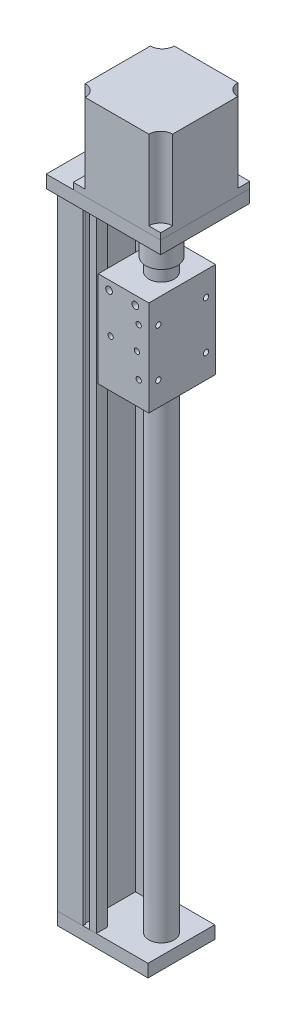
SolidWorks part; units mm, degrees
ref_plane "Front Plane" through (0, 0, 0) normal (0, 0, 1) x (1, 0, 0)
ref_plane "Top Plane" through (0, 0, 0) normal (0, 1, 0) x (1, 0, 0)
ref_plane "Right Plane" through (0, 0, 0) normal (1, 0, 0) x (0, 0, -1)
sketch "Sketch1" plane through (0, 0, 0) normal (0, 1, 0) x (1, 0, 0)
  line L1 (0, 21) -> (57, 21)
  line L2 (0, 21) -> (0, -21)
  line L3 (0, -21) -> (57, -21)
  line L4 (57, 21) -> (57, -21)
  point P4 (0, 0)
  dimension "D1" = 57
  dimension "D2" = 42
extrude "Boss-Extrude1" add sketch "Sketch1" along normal blind 8
sketch "Sketch2" plane through (0, 8, 0) normal (0, 1, 0) x (1, 0, 0)
  line L0 (0, 21) -> (0, -21)
  line L1 (0, -21) -> (24.5, -21)
  line L2 (0, -21) -> (57, -21) construction
  line L3 (24.5, -21) -> (24.5, -14)
  line L4 (24.5, -14) -> (14.1, -14)
  line L5 (14.1, -14) -> (14.1, 14)
  line L6 (14.1, 14) -> (24.5, 14)
  line L7 (24.5, 14) -> (24.5, 21)
  line L8 (57, 21) -> (0, 21) construction
  line L9 (24.5, 21) -> (0, 21)
  dimension "D1" = 24.5
  dimension "D2" = 7
  dimension "D3" = 10.4
extrude "Boss-Extrude2" add sketch "Sketch2" along normal blind 397
sketch "Sketch3" plane through (0, 405, 0) normal (0, 1, 0) x (1, 0, 0)
  line L1 (0, 28) -> (72, 28)
  line L2 (0, 28) -> (0, -28)
  line L3 (0, -28) -> (72, -28)
  line L4 (72, 28) -> (72, -28)
  point P4 (0, 0)
  dimension "D1" = 56
  dimension "D2" = 72
extrude "Boss-Extrude3" add sketch "Sketch3" along normal blind 8
sketch "Sketch4" plane through (0, 413, 0) normal (0, 1, 0) x (1, 0, 0)
  line L0 (0, -28) -> (72, -28) construction
  line L1 (72, 28) -> (17, 28)
  line L2 (72, 28) -> (72, -28)
  line L3 (72, -28) -> (17, -28)
  line L4 (17, 28) -> (17, -28)
  line L5 (57, -21) -> (57, 21) construction
  line L6 (57, -21) -> (57, 21) construction
  point P7 (44.5, 28)
  dimension "D1" = 55
extrude "Boss-Extrude4" add sketch "Sketch4" along normal blind 54
sketch "Sketch5" plane through (0, 467, 0) normal (0, 1, 0) x (1, 0, 0)
  line L0 (17, 28) -> (17, 20.5)
  line L1 (17, 28) -> (17, -28) construction
  line L2 (17, 28) -> (24.5, 28)
  line L3 (44.5, 28) -> (44.5, 12.3616) construction
  line L4 (72, 28) -> (17, 28) construction
  line L5 (72, 28) -> (64.5, 28)
  line L6 (72, 28) -> (72, 20.5)
  line L7 (17, 0) -> (32.1173, 0) construction
  line L8 (72, -28) -> (72, -20.5)
  line L9 (72, -28) -> (64.5, -28)
  line L10 (17, -28) -> (24.5, -28)
  line L11 (17, -28) -> (17, -20.5)
  arc A0 (24.5, 28) -> (17, 20.5) centre (17, 28) cw
  arc A1 (64.5, 28) -> (72, 20.5) centre (72, 28) ccw
  arc A2 (64.5, -28) -> (72, -20.5) centre (72, -28) cw
  arc A3 (24.5, -28) -> (17, -20.5) centre (17, -28) ccw
  dimension "D1" = 7.5
extrude "Cut-Extrude1" cut sketch "Sketch5" against normal blind 50
sketch "Sketch6" plane through (0, 8, 0) normal (0, 1, 0) x (1, 0, 0)
  line L0 (57, -21) -> (57, 21) construction
  circle A0 centre (44.5, 0) radius 8
  point P5 (0, 0)
  dimension "D1" = 16
  dimension "D2" = 12.5
extrude "Boss-Extrude5" add sketch "Sketch6" along normal blind 368.3
ref_plane "Plane1" through (0, 338, 0) normal (0, 1, 0) x (1, 0, 0)
sketch "Sketch7" plane through (0, 338, 0) normal (0, 1, 0) x (1, 0, 0)
  line L0 (24.5, -21) -> (24.5, -14) construction
  line L1 (25.7, -21) -> (57.5, -21)
  line L2 (25.7, -21) -> (25.7, 21)
  line L3 (25.7, 21) -> (57.5, 21)
  line L4 (57.5, -21) -> (57.5, 21)
  line L5 (24.5, -21) -> (57, -21) construction
  line L6 (57, 21) -> (24.5, 21) construction
  line L7 (0, 21) -> (0, -21) construction
  dimension "D1" = 1.2
  dimension "D2" = 57.5
extrude "Boss-Extrude6" add sketch "Sketch7" along normal mid plane 60
sketch "Sketch8" plane through (0, 376.3, 0) normal (0, 1, 0) x (1, 0, 0)
  circle A0 centre (44.5, 0) radius 10
  dimension "D1" = 20
extrude "Boss-Extrude7" add sketch "Sketch8" along normal blind 25
sketch "Sketch9" plane through (0, 405, 0) normal (0, -1, 0) x (1, 0, 0)
  circle A0 centre (44.5, 0) radius 15
  circle A1 centre (44.5, 0) radius 10
  circle A2 centre (44.5, 0) radius 10 construction
  dimension "D2" = 30
  dimension "D1" = 0
extrude "Cut-Extrude2" cut sketch "Sketch9" against normal blind 5
sketch "Sketch10" plane through (0, 401.3, 0) normal (0, 1, 0) x (1, 0, 0)
  circle A0 centre (44.5, 0) radius 3.175
  dimension "D1" = 6.35
extrude "Boss-Extrude8" add sketch "Sketch10" along normal up to next
sketch "Sketch11" plane through (0, 0, -21) normal (0, 0, -1) x (-1, 0, 0)
  line L0 (-24.5, 405) -> (0, 405) construction
  line L1 (-20.3, 405) -> (-16, 405)
  line L2 (-20.3, 405) -> (-20.3, 8)
  line L3 (-20.3, 8) -> (-16, 8)
  line L4 (-16, 405) -> (-16, 8)
  line L5 (-57, 8) -> (-24.5, 8) construction
  line L6 (0, 405) -> (0, 0) construction
  dimension "D1" = 16
  dimension "D2" = 4.3
extrude "Cut-Extrude3" cut sketch "Sketch11" against normal blind 5.4
ref_plane "Plane2" through (18.15, 0, 0) normal (1, 0, 0) x (0, 0, -1)
sketch "Sketch12" plane through (18.15, 0, 0) normal (1, 0, 0) x (0, 0, -1)
  line L0 (15.6, 405) -> (15.6, 8) construction
  line L1 (19.2, 8) -> (15.6, 8)
  line L2 (19.2, 8) -> (19.2, 405)
  line L3 (19.2, 405) -> (15.6, 405)
  line L4 (15.6, 8) -> (15.6, 405)
  line L5 (28, 405) -> (21, 405) construction
  line L6 (15.6, 8) -> (21, 8) construction
  line L7 (21, 405) -> (21, 8) construction
  dimension "D1" = 1.8
extrude "Cut-Extrude4" cut sketch "Sketch12" against normal mid plane 5.4
mirror "Mirror1" about plane through (0, 0, 0) normal (0, 0, 1) of "Cut-Extrude3", "Cut-Extrude4"
sketch "Sketch13" plane through (0, 0, 0) normal (-1, 0, 0) x (0, 0, 1)
  line L0 (21, 8) -> (-21, 8) construction
  line L1 (21, 8) -> (-21, 8) construction
  line L3 (17.15, 405) -> (12.85, 405)
  line L4 (17.15, 405) -> (17.15, 8)
  line L5 (17.15, 8) -> (12.85, 8)
  line L6 (12.85, 405) -> (12.85, 8)
  line L7 (21, 405) -> (28, 405) construction
  line L8 (0, 413) -> (0, 348.5706) construction
  line L9 (-28, 413) -> (28, 413) construction
  point P17 (15, 405)
  dimension "D1" = 15
  dimension "D2" = 4.3
extrude "Cut-Extrude5" cut sketch "Sketch13" against normal blind 6.8
ref_plane "Plane3" through (0, 0, 15) normal (0, 0, 1) x (1, 0, 0)
sketch "Sketch14" plane through (0, 0, 15) normal (0, 0, 1) x (1, 0, 0)
  line L0 (6.8, 405) -> (0, 405) construction
  line L1 (2, 8) -> (5.3, 8)
  line L2 (2, 8) -> (2, 405)
  line L3 (2, 405) -> (5.3, 405)
  line L4 (5.3, 8) -> (5.3, 405)
  line L5 (6.8, 8) -> (0, 8) construction
  line L6 (6.8, 405) -> (6.8, 8) construction
  line L7 (0, 405) -> (0, 8) construction
  dimension "D1" = 1.5
  dimension "D2" = 2
extrude "Cut-Extrude6" cut sketch "Sketch14" against normal mid plane 6.8
mirror "Mirror2" about plane through (0, 0, 0) normal (0, 0, 1) of "Cut-Extrude6", "Cut-Extrude5"
sketch "Sketch15" plane through (57.5, 0, 0) normal (1, 0, 0) x (0, 0, -1)
  line L0 (-21, 368) -> (21, 368) construction
  line L1 (-15, 323) -> (15, 323)
  line L2 (-15, 323) -> (-15, 353)
  line L3 (-15, 353) -> (15, 353)
  line L4 (15, 323) -> (15, 353)
  line L5 (-15, 323) -> (15, 353) construction
  line L6 (-15, 353) -> (15, 323) construction
  line L7 (-21, 368) -> (-21, 308) construction
  point P0 (0, 338)
  point P5 (0, 368)
  point P6 (-21, 338)
  dimension "D1" = 30
  dimension "D2" = 30
hole_wizard "M4x0.7 Tapped Hole1" positions "Sketch19" profile "Sketch18" tap size "M4x0.7" standard "ANSI Metric"
sketch "Sketch19" plane through (57.5, 0, 0) normal (1, 0, 0) x (0, 0, -1)
  point P0 (-15, 353)
  point P3 (15, 353)
  point P6 (15, 323)
  point P9 (-15, 323)
sketch "Sketch18" plane through (57.5, 353, 15) normal (0, 1, 0) x (0, 0, -1)
  line L0 (0, 0) -> (0, 11.0914)
  line L1 (0, 11.0914) -> (1.65, 10.1)
  line L2 (1.65, 10.1) -> (1.65, 0)
  line L5 (1.65, 0) -> (0, 0)
  line L10 (0, 11.0914) -> (-1.65, 10.1) construction
  line L11 (0, -6.35) -> (0, 107.95) construction
  dimension "Tap Drill Dia." = 3.3
  dimension "Tap Drill Depth" = 10.1
  dimension "Drill Angle" = 118
cosmetic thread "Hole Thread1" parameters "D1"=8, "D2"=4
cosmetic thread "Hole Thread2" parameters "D1"=8, "D2"=4
cosmetic thread "Hole Thread3" parameters "D1"=8, "D2"=4
cosmetic thread "Hole Thread4" parameters "D1"=8, "D2"=4
ref_plane "Plane5" through (0, 8, 0) normal (0, 1, 0) x (1, 0, 0)
ref_plane "Plane6" through (0, 413, 0) normal (0, 1, 0) x (1, 0, 0)
ref_plane "Plane7" through (0, 405, 0) normal (0, -1, 0) x (-1, 0, 0)
split line "Split Line4"
split line "Split Line5"
split line "Split Line6"
sketch "Sketch20" plane through (0, 0, 0) normal (0, 0, 1) x (1, 0, 0)
  line L0 (36.5, 376.3) -> (52.5, 376.3) construction
  line L1 (27, 368) -> (62, 368) construction
  line L2 (27, 368) -> (27, 308) construction
  line L3 (27, 308) -> (62, 308) construction
  line L4 (62, 368) -> (62, 308) construction
  line L5 (24.5, 8) -> (57, 8) construction
  line L6 (27, 68) -> (62, 68) construction
  line L7 (27, 68) -> (27, 8) construction
  line L8 (27, 8) -> (62, 8) construction
  line L9 (62, 68) -> (62, 8) construction
  line L10 (44.5, 368) -> (44.5, 68) construction
  line L11 (44.5, 218) -> (94.5, 218)
  line L12 (44.5, 228) -> (94.5, 228) construction
  line L13 (44.5, 208) -> (94.5, 208) construction
  point P4 (44.5, 376.3)
  point P5 (62, 338)
  point P12 (44.5, 68)
  point P19 (62, 38)
  dimension "D1" = 60
  dimension "D2" = 60
  dimension "D3" = 300
  dimension "D4" = 35
  dimension "D5" = 10
  dimension "D6" = 50
  dimension "D7" = 10
sketch "Sketch21" plane through (0, 0, 0) normal (0, 0, 1) x (1, 0, 0)
  line L0 (44.5, 308) -> (44.5, 13.0745) construction
  line L1 (59.5, 89.55) -> (29.5, 89.55)
  line L2 (59.5, 89.55) -> (59.5, 29.55)
  line L3 (59.5, 29.55) -> (29.5, 29.55)
  line L4 (29.5, 89.55) -> (29.5, 29.55)
  line L5 (36.5, 308) -> (52.5, 308) construction
  line L6 (24.5, 8) -> (57, 8) construction
  line L7 (59.5, 329.55) -> (59.5, 59.55) construction
  line L8 (29.5, 359.55) -> (59.5, 359.55)
  line L9 (29.5, 359.55) -> (29.5, 299.55)
  line L10 (29.5, 299.55) -> (59.5, 299.55)
  line L11 (59.5, 359.55) -> (59.5, 299.55)
  line L12 (59.5, 194.55) -> (259.5525, 194.55) construction
  point P8 (44.5, 89.55)
  point P11 (59.5, 59.55)
  point P16 (44.5, 359.55)
  point P17 (59.5, 329.55)
  dimension "D1" = 60
  dimension "D2" = 30
  dimension "D3" = 51.55
  dimension "D4" = 270
sketch "Sketch22" plane through (0, 0, 21) normal (0, 0, 1) x (1, 0, 0)
  line L0 (57.5, 338) -> (25.7, 338) construction
  line L1 (57.5, 368) -> (57.5, 308) construction
  line L2 (25.7, 368) -> (25.7, 308) construction
  line L3 (57.5, 353) -> (25.7, 353) construction
  line L4 (25.7, 368) -> (57.5, 368) construction
  point P8 (51.15, 353)
  point P9 (50, 338)
  point P10 (33.5, 338)
  point P11 (51.15, 323)
  point P12 (49, 362.5)
  point P13 (32.5, 362.5)
  dimension "D1" = 30
  dimension "D2" = 6.35
  dimension "D3" = 7.5
  dimension "D4" = 16.5
  dimension "D5" = 8.5
  dimension "D6" = 16.5
  dimension "D7" = 5.5
hole_wizard "M4x0.7 Tapped Hole2" positions "Sketch22" profile "Sketch23" tap size "M4x0.7" standard "ANSI Metric"
sketch "Sketch23" plane through (51.15, 323, 21) normal (1, 0, 0) x (0, -1, 0)
  line L0 (0, 0) -> (0, 6.9914)
  line L1 (0, 6.9914) -> (1.65, 6)
  line L2 (1.65, 6) -> (1.65, 0)
  line L5 (1.65, 0) -> (0, 0)
  line L10 (0, 6.9914) -> (-1.65, 6) construction
  line L11 (0, -6.35) -> (0, 107.95) construction
  dimension "Tap Drill Dia." = 3.3
  dimension "Tap Drill Depth" = 6
  dimension "Drill Angle" = 118
cosmetic thread "Hole Thread5" parameters "D1"=8, "D2"=4
cosmetic thread "Hole Thread6" parameters "D1"=8, "D2"=4
cosmetic thread "Hole Thread7" parameters "D1"=8, "D2"=4
cosmetic thread "Hole Thread8" parameters "D1"=8, "D2"=4
sketch "Sketch24" plane through (0, 0, 21) normal (0, 0, 1) x (1, 0, 0)
  line L0 (49, 362.5) -> (32.5, 362.5) construction
  line L1 (57.5, 368) -> (57.5, 308) construction
  line L2 (25.7, 368) -> (57.5, 368) construction
  point P0 (49, 362.5)
  point P1 (32.5, 362.5)
  point P10 (49, 362.5)
  point P13 (32.5, 362.5)
  dimension "D1" = 8.5
  dimension "D2" = 16.5
  dimension "D3" = 5.5
hole_wizard "M5x0.8 Tapped Hole1" positions "Sketch24" profile "Sketch25" tap size "M5x0.8" standard "ANSI Metric"
sketch "Sketch25" plane through (32.5, 362.5, 21) normal (1, 0, 0) x (0, -1, 0)
  line L0 (0, 0) -> (0, 11.2618)
  line L1 (0, 11.2618) -> (2.1, 10)
  line L2 (2.1, 10) -> (2.1, 0)
  line L5 (2.1, 0) -> (0, 0)
  line L10 (0, 11.2618) -> (-2.1, 10) construction
  line L11 (0, -6.35) -> (0, 107.95) construction
  dimension "Tap Drill Dia." = 4.2
  dimension "Tap Drill Depth" = 10
  dimension "Drill Angle" = 118
cosmetic thread "Hole Thread9" parameters "D1"=10, "D2"=5
cosmetic thread "Hole Thread10" parameters "D1"=10, "D2"=5
mirror "Mirror3" about plane through (0, 0, 0) normal (0, 0, 1) of "M5x0.8 Tapped Hole1", "M4x0.7 Tapped Hole2"
cosmetic thread "Hole Thread11" parameters "D1"=10, "D2"=5
cosmetic thread "Hole Thread12" parameters "D1"=8, "D2"=4
cosmetic thread "Hole Thread13" parameters "D1"=8, "D2"=4
cosmetic thread "Hole Thread14" parameters "D1"=10, "D2"=5
cosmetic thread "Hole Thread15" parameters "D1"=8, "D2"=4
cosmetic thread "Hole Thread16" parameters "D1"=8, "D2"=4
equation "\"D2@Sketch15\"=\"D1@Sketch15\""
equation "\"D7@Sketch20\"=\"D5@Sketch20\""
